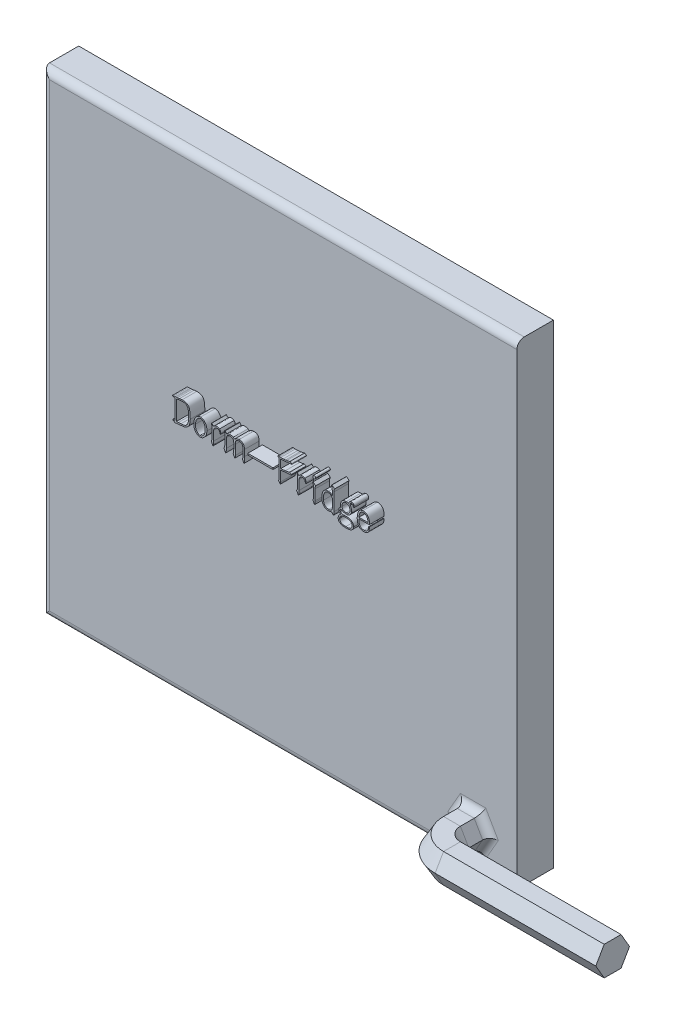
SolidWorks part; units mm, degrees
ref_plane "前视基准面" through (0, 0, 0) normal (0, 0, 1) x (1, 0, 0)
ref_plane "上视基准面" through (0, 0, 0) normal (0, 1, 0) x (1, 0, 0)
ref_plane "右视基准面" through (0, 0, 0) normal (1, 0, 0) x (0, 0, -1)
sketch "Sketch1" plane through (0, 0, 0) normal (0, 0, 1) x (1, 0, 0)
  line L1 (-32.5, -32.5) -> (32.5, -32.5)
  line L2 (-32.5, -32.5) -> (-32.5, 32.5)
  line L3 (-32.5, 32.5) -> (32.5, 32.5)
  line L4 (32.5, -32.5) -> (32.5, 32.5)
  line L5 (-32.5, -32.5) -> (32.5, 32.5) construction
  line L6 (-32.5, 32.5) -> (32.5, -32.5) construction
  point P0 (0, 0)
  dimension "D1" = 65
  dimension "D2" = 65
extrude "Extrude1" add sketch "Sketch1" along normal blind 5
sketch3d "3DSketch2"
  line L0 (26.5, -28, 4.8902) -> (26.5, -28, 7.8902)
  line L1 (29.5, -28, 10.8902) -> (51.5, -28, 10.8902)
  arc A0 (29.5, -28, 10.8902) -> (26.5, -28, 7.8902) centre (29.5, -28, 7.8902) ccw
  point P3 (32.5, -28, 5)
  point P7 (26.5, -28, 10.8902)
  point P8 (29.5, -31, 7.8902)
  point P9 (0, 0, 0)
  dimension "D4" = 3
  dimension "D1" = 6
  dimension "D2" = 6
  dimension "D3" = 25
sketch "Sketch3" plane through (0, 0, 5) normal (0, 0, 1) x (1, 0, 0)
  line L7 (28.8094, -28) -> (27.6547, -26)
  line L8 (27.6547, -26) -> (25.3453, -26)
  line L9 (25.3453, -26) -> (24.1906, -28)
  line L10 (24.1906, -28) -> (25.3453, -30)
  line L11 (25.3453, -30) -> (27.6547, -30)
  line L12 (27.6547, -30) -> (28.8094, -28)
  circle A0 centre (26.5, -28) radius 2 construction
sweep "Sweep1" add profiles "Sketch3" path "3DSketch2"
fillet "Fillet2" radius 1 6 edges at (24.7679, -29, 5) (24.7679, -27, 5) (26.5, -26, 5) (28.2321, -27, 5) (28.2321, -29, 5) (26.5, -30, 5)
sketch "Sketch4" plane through (0, 0, 5) normal (0, 0, 1) x (1, 0, 0)
  text T0 "Dorm-Fridge" font "汉仪长仿宋体" height 3.5
extrude "Extrude2" add sketch "Sketch4" along normal blind 2
fillet "Fillet3" radius 1 3 edges at (0, -32.5, 5) (0, 32.5, 5) (-32.5, 0, 5)
